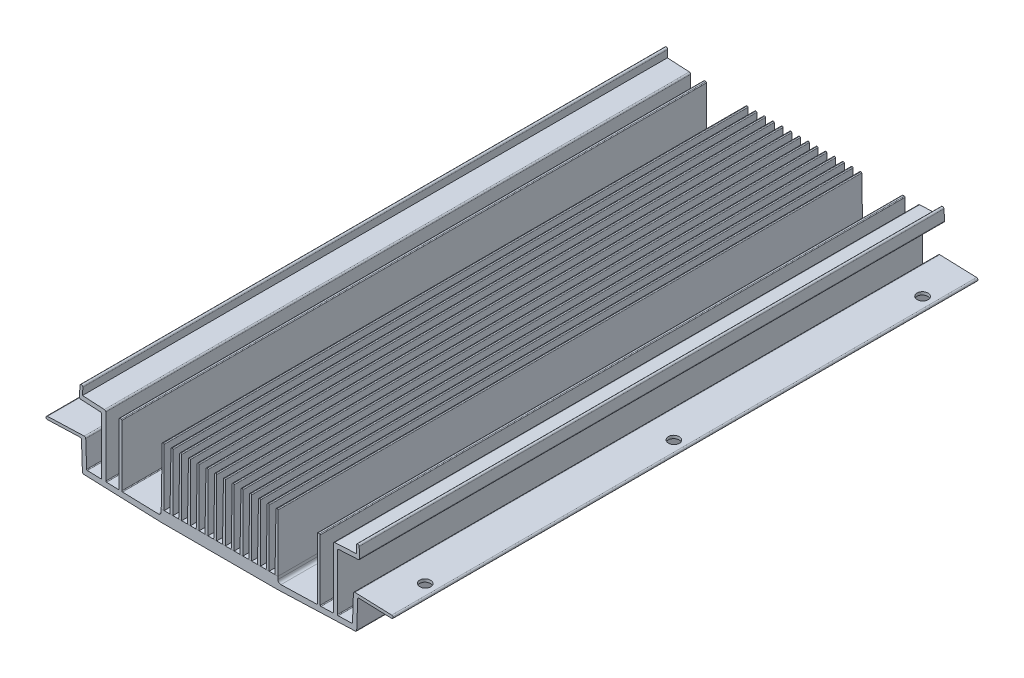
SolidWorks part; units mm, degrees
material "6061 Alloy"
ref_plane "Front Plane" through (0, 0, 0) normal (0, 0, 1) x (1, 0, 0)
ref_plane "Top Plane" through (0, 0, 0) normal (0, 1, 0) x (1, 0, 0)
ref_plane "Right Plane" through (0, 0, 0) normal (1, 0, 0) x (0, 0, -1)
sketch "Sketch1" plane through (0, 0, 0) normal (0, 0, 1) x (1, 0, 0)
  line L0 (-59.5, 12) -> (59.5, 12) construction
  line L1 (-47, 0) -> (47, 0) construction
  line L2 (-59.0174, 11.9873) -> (-45.8988, 12.4454)
  line L3 (-45.8988, 12.4454) -> (-45.5601, 2.7479)
  line L4 (-58.9826, 10.9879) -> (-47.363, 11.3937)
  line L5 (-47.363, 11.3937) -> (-47, 1)
  line L6 (-47, 1) -> (-20, 0)
  line L7 (0, 0) -> (0, 71.8398) construction
  line L8 (47, 1) -> (20, 0)
  line L9 (-20, 0) -> (20, 0)
  line L10 (-59.0174, 11.9873) -> (-58.9826, 10.9879) construction
  line L11 (-59.5, 12) -> (-59.5, 69.9263) construction
  line L12 (-45.5601, 2.7479) -> (-40.4, 2.5969)
  line L13 (-20, 2) -> (-20, 4)
  line L14 (-20, 4) -> (20, 4)
  line L15 (47.363, 11.3937) -> (47, 1)
  line L16 (58.9826, 10.9879) -> (47.363, 11.3937)
  line L17 (59.0174, 11.9873) -> (45.8988, 12.4454)
  line L18 (45.8988, 12.4454) -> (45.5601, 2.7479)
  line L19 (45.5601, 2.7479) -> (40.4, 2.5969)
  line L20 (20, 2) -> (20, 4)
  line L21 (-33.5, 2.395) -> (-33.5, 23.75)
  line L22 (-33.5, 23.75) -> (-34.5, 23.75)
  line L23 (-34.5, 23.75) -> (-34.5, 2.4243)
  line L24 (-33.5, 2.395) -> (-20, 2)
  line L25 (-67.1747, 23.75) -> (67.1747, 23.75) construction
  line L26 (-39, 2.556) -> (-39, 23.75)
  line L31 (33.5, 2.395) -> (20, 2)
  line L32 (39, 2.556) -> (34.5, 2.4243)
  line L33 (-40.4, 22.3714) -> (-40.4, 2.5969)
  line L34 (-39, 2.556) -> (-34.5, 2.4243)
  line L35 (-40.4, 22.3714) -> (-48.0636, 22.773)
  line L36 (-48.0636, 22.773) -> (-47.8542, 26.7675)
  line L38 (-46.8556, 26.7152) -> (-46.989, 24.1687)
  line L39 (-46.989, 24.1687) -> (-39, 23.75)
  line L40 (46.989, 24.1687) -> (39, 23.75)
  line L42 (46.8556, 26.7152) -> (46.989, 24.1687)
  line L43 (48.0636, 22.773) -> (47.8542, 26.7675)
  line L44 (40.4, 22.3714) -> (48.0636, 22.773)
  line L45 (40.4, 22.3714) -> (40.4, 2.5969)
  line L46 (39, 2.556) -> (39, 23.75)
  line L47 (33.5, 23.75) -> (34.5, 23.75)
  line L48 (34.5, 23.75) -> (34.5, 2.4243)
  line L49 (33.5, 2.395) -> (33.5, 23.75)
  arc A0 (-59.0174, 11.9873) -> (-58.9826, 10.9879) centre (-59, 11.4876) ccw
  arc A1 (59.0174, 11.9873) -> (58.9826, 10.9879) centre (59, 11.4876) cw
  arc A2 (-47.8542, 26.7675) -> (-46.8556, 26.7152) centre (-47.3549, 26.7414) cw
  arc A3 (47.8542, 26.7675) -> (46.8556, 26.7152) centre (47.3549, 26.7414) ccw
  point P2 (0, 12)
  point P35 (0, 4)
  point P38 (-34, 23.75)
  point P40 (0, 23.75)
  dimension "D20" = 4
  dimension "D1" = 119
  dimension "D2" = 12
  dimension "D3" = 94
  dimension "D4" = 1
  dimension "D5" = 40
  dimension "D6" = 88
  dimension "D7" = 1
  dimension "D8" = 1.5
  dimension "D9" = 11.4
  dimension "D10" = 4
  dimension "D11" = 2
  dimension "D12" = 1.8
  dimension "D13" = 13.5
  dimension "D14" = 1
  dimension "D15" = 23.75
  dimension "D16" = 4.5
  dimension "D17" = 1.4
  dimension "D18" = 1.45
  dimension "D19" = 1
  dimension "D21" = 3
  dimension "D22" = 9
extrude "Boss-Extrude1" add sketch "Sketch1" along normal blind 200.5
sketch "Sketch3" plane through (0, 4, 0) normal (0, 1, 0) x (1, 0, 0)
  line L0 (20, 0) -> (-20, 0) construction
  line L1 (-19, 0) -> (-20, 0)
  line L2 (-19, 0) -> (-19, -200.5)
  line L3 (-19, -200.5) -> (-20, -200.5)
  line L4 (-20, 0) -> (-20, -200.5)
  dimension "D1" = 1
extrude "Boss-Extrude2" add sketch "Sketch3" along normal up to surface (19.75 mm away) draft 0.5
fillet "Fillet5" radius 0.3 2 edges at (-19.1724, 23.75, 100.25) (-19.8276, 23.75, 100.25)
pattern_linear "LPattern1" count 14 spacing 3 along (1, 0, 0) of "Boss-Extrude2", "Fillet5"
fillet "Fillet1" radius 1 2 edges at (20, 2, 100.25) (-20, 2, 100.25)
fillet "Fillet2" radius 0.5 12 edges at (39, 23.75, 100.25) (-39, 23.75, 100.25) (-45.8988, 12.4454, 100.25) (45.8988, 12.4454, 100.25) (48.0636, 22.773, 100.25) (40.4, 22.3714, 100.25) (47.363, 11.3937, 100.25) (47, 1, 100.25) (-48.0636, 22.773, 100.25) (-40.4, 22.3714, 100.25) (-47.363, 11.3937, 100.25) (-47, 1, 100.25)
fillet "Fillet4" radius 0.25 14 edges at (-45.5601, 2.7479, 100.25) (-33.5, 2.395, 100.25) (-34.5, 2.4243, 100.25) (-40.4, 2.5969, 100.25) (-39, 2.556, 100.25) (45.5601, 2.7479, 100.25) (40.4, 2.5969, 100.25) (39, 2.556, 100.25) (34.5, 2.4243, 100.25) (33.5, 2.395, 100.25) (34.5, 23.75, 100.25) (33.5, 23.75, 100.25) (-33.5, 23.75, 100.25) (-34.5, 23.75, 100.25)
hole_wizard "CSK for #6 Flat Head Socket Cap Screw" positions "Sketch4" profile "Sketch5" countersink size "#6" standard "ANSI Inch"
sketch "Sketch4" plane through (-59.5, -7, 134.2497) normal (0, -1, 0) x (0, 0, 1)
  point P0 (-119.2497, 115)
  point P3 (-33.9997, 115)
  point P6 (51.2503, 115)
  point P9 (51.2503, -115)
  point P12 (-33.9997, -115)
  point P15 (-119.2497, -115)
sketch "Sketch5" plane through (-174.5, -7, 15) normal (1, 0, 0) x (0, 0, -1)
  line L0 (0, 0) -> (0, 21.1408)
  line L1 (0, 21.1408) -> (1.8986, 20)
  line L2 (1.8986, 20) -> (1.8986, 2.301)
  line L3 (1.8986, 2.301) -> (3.8989, 0)
  line L4 (3.8989, 0) -> (0, 0)
  line L5 (-1.8986, 2.301) -> (-3.8989, 0) construction
  line L6 (0, 21.1408) -> (-1.8987, 20) construction
  line L7 (0, -6.35) -> (0, 107.95) construction
  dimension "Hole Dia." = 3.7973
  dimension "Hole Depth" = 20
  dimension "Near C'Sink Dia." = 7.7978
  dimension "Near C'Sink Angle" = 82
  dimension "Drill Angle" = 118
hole_wizard "CSK for #6 Flat Head Socket Cap Screw" positions "Sketch6" profile "Sketch7" countersink size "#6" standard "ANSI Inch"
sketch "Sketch6" plane through (59.5, -7, 134.2497) normal (0, -1, 0) x (0, 0, 1)
  point P0 (-119.2497, 115)
  point P3 (-33.9997, 115)
  point P6 (51.2503, 115)
  point P9 (51.2503, -115)
  point P12 (-33.9997, -115)
  point P15 (-119.2497, -115)
sketch "Sketch7" plane through (-55.5, -7, 15) normal (1, 0, 0) x (0, 0, -1)
  line L0 (0, 0) -> (0, 21.1408)
  line L1 (0, 21.1408) -> (1.8986, 20)
  line L2 (1.8986, 20) -> (1.8986, 2.301)
  line L3 (1.8986, 2.301) -> (3.8989, 0)
  line L4 (3.8989, 0) -> (0, 0)
  line L5 (-1.8986, 2.301) -> (-3.8989, 0) construction
  line L6 (0, 21.1408) -> (-1.8987, 20) construction
  line L7 (0, -6.35) -> (0, 107.95) construction
  dimension "Hole Dia." = 3.7973
  dimension "Hole Depth" = 20
  dimension "Near C'Sink Dia." = 7.7978
  dimension "Near C'Sink Angle" = 82
  dimension "Drill Angle" = 118
